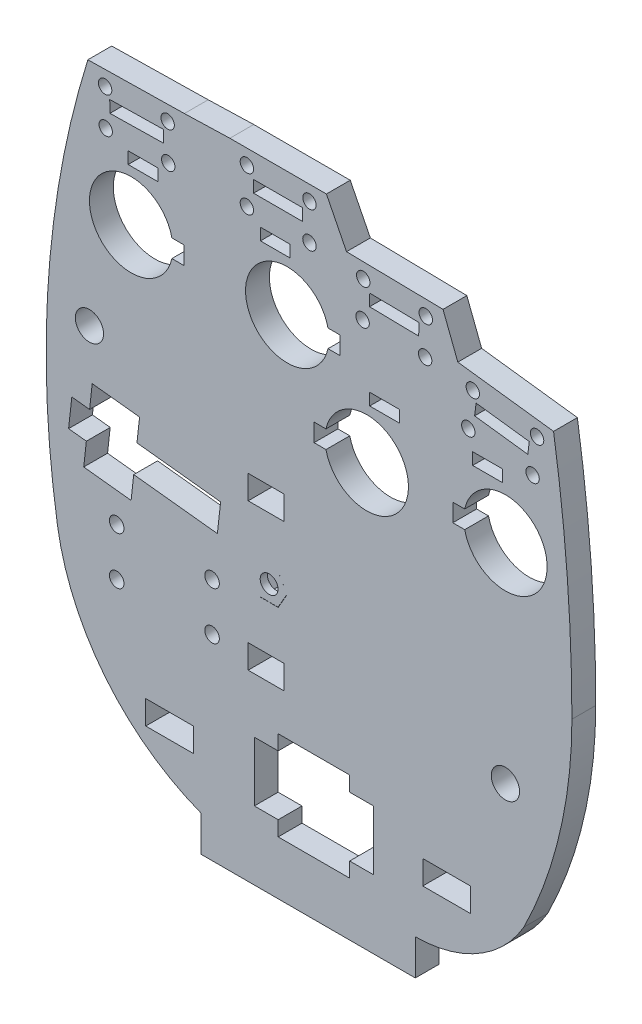
SolidWorks part; units mm, degrees
ref_plane "Front Plane" through (0, 0, 0) normal (0, 0, 1) x (1, 0, 0)
ref_plane "Top Plane" through (0, 0, 0) normal (0, 1, 0) x (1, 0, 0)
ref_plane "Right Plane" through (0, 0, 0) normal (1, 0, 0) x (0, 0, -1)
sketch "Sketch1" plane through (0, 0, 0) normal (0, 0, 1) x (1, 0, 0)
  line L0 (-4.125, 78.51) -> (-4.125, 76.51)
  line L1 (4.125, 78.51) -> (-4.125, 78.51)
  line L2 (-12.9786, -18) -> (-12.9786, -24)
  line L3 (-10.203, 23.9877) -> (-9.6615, 28.8655)
  line L4 (-4.125, 76.51) -> (4.125, 76.51)
  line L5 (4.125, 76.51) -> (4.125, 78.51)
  line L6 (-35.1781, 26.7603) -> (-34.6366, 31.6381)
  line L7 (10.3588, 63.1512) -> (10.3588, 60.1512)
  line L8 (-8.1, 82.51) -> (8.1, 82.51)
  line L9 (8.3588, 63.1512) -> (10.3588, 63.1512)
  line L10 (11.4712, 75.8064) -> (27.6688, 75.5236)
  line L11 (32.6473, 57.3216) -> (37.6473, 57.3216)
  line L12 (0, 0) -> (-23.845, 0) construction
  line L13 (10.3588, 60.1512) -> (8.3588, 60.1512)
  line L14 (-17.8416, 63.1512) -> (-15.8416, 63.1512)
  line L15 (-15.8416, 63.1512) -> (-15.8416, 60.1512)
  line L16 (-15.8416, 60.1512) -> (-17.8416, 60.1512)
  line L17 (32.6473, 55.3216) -> (37.6473, 55.3216)
  line L18 (37.6473, 55.3216) -> (37.6473, 57.3216)
  line L19 (32.6473, 57.3216) -> (32.6473, 55.3216)
  line L20 (-28.2745, 78.062) -> (-19.2758, 78.2192)
  line L21 (-28.2745, 78.062) -> (-28.2395, 76.0623)
  line L22 (-10.0543, 52.8756) -> (-18.0543, 52.8756) construction
  line L23 (-9.6615, 28.8655) -> (-23.7037, 30.4244)
  line L24 (-28.2395, 76.0623) -> (-19.2408, 76.2195)
  line L25 (-24.6866, 21.571) -> (-32.6377, 22.4537)
  line L26 (-32.6377, 22.4537) -> (-32.1964, 26.4293)
  line L27 (-24.2452, 25.5466) -> (-10.203, 23.9877)
  line L28 (-19.2408, 76.2195) -> (-19.2758, 78.2192)
  line L29 (15.3631, 57.3216) -> (20.3631, 57.3216)
  line L30 (15.3631, 55.3216) -> (20.3631, 55.3216)
  line L31 (-12.9786, -24) -> (23.0214, -24)
  line L32 (20.3631, 55.3216) -> (20.3631, 57.3216)
  line L33 (23.0214, -24) -> (23.0214, -18)
  line L34 (15.3631, 57.3216) -> (15.3631, 55.3216)
  line L35 (-2.9786, 72.1512) -> (2.0214, 72.1512)
  line L36 (15.3758, 71.7376) -> (15.3409, 69.7379)
  line L37 (15.3409, 69.7379) -> (23.5897, 69.5939)
  line L38 (8.0257, 48.3216) -> (6.0257, 48.3216)
  line L39 (-2.9786, 70.1512) -> (2.0214, 70.1512)
  line L40 (23.6246, 71.5936) -> (15.3758, 71.7376)
  line L41 (6.0257, 48.3216) -> (6.0257, 45.3216)
  line L42 (23.5897, 69.5939) -> (23.6246, 71.5936)
  line L43 (-23.845, 0) -> (-23.845, 82.14) construction
  line L44 (2.0214, 70.1512) -> (2.0214, 72.1512)
  line L45 (19.57, 75.665) -> (19.6234, 78.7251) construction
  line L46 (-2.9786, 72.1512) -> (-2.9786, 70.1512)
  line L47 (42.1536, 63.5476) -> (33.2239, 64.6755)
  line L48 (6.0257, 45.3216) -> (8.0257, 45.3216)
  line L49 (29.3099, 45.3216) -> (31.3099, 45.3216)
  line L50 (29.3099, 48.3216) -> (29.3099, 45.3216)
  line L51 (31.3099, 48.3216) -> (29.3099, 48.3216)
  line L52 (-23.2624, 34.3999) -> (-31.2135, 35.2826)
  line L53 (33.2239, 64.6755) -> (32.9732, 62.6912)
  line L54 (-25.179, 72.1512) -> (-20.179, 72.1512)
  line L55 (-31.9438, 81.9985) -> (-15.7462, 82.2815)
  line L56 (46.2262, 67.065) -> (30.1538, 69.095)
  line L57 (-25.179, 70.1512) -> (-20.179, 70.1512)
  line L58 (32.9732, 62.6912) -> (41.903, 61.5633)
  line L59 (-20.179, 70.1512) -> (-20.179, 72.1512)
  line L60 (-25.179, 72.1512) -> (-25.179, 70.1512)
  line L61 (41.903, 61.5633) -> (42.1536, 63.5476)
  line L62 (-35.1781, 26.7603) -> (-32.1964, 26.4293)
  line L63 (-4, -2.5) -> (0, -2.5)
  line L64 (12, 0) -> (0, 0)
  line L65 (12, 0) -> (12, -2.5)
  line L66 (12, -15) -> (0, -15)
  line L67 (-31.2135, 35.2826) -> (-31.6549, 31.3071)
  line L68 (-23.7037, 30.4244) -> (-23.2624, 34.3999)
  line L69 (-34.6366, 31.6381) -> (-31.6549, 31.3071)
  line L70 (-24.6866, 21.571) -> (-24.2452, 25.5466)
  line L71 (16, -7.5) -> (41.235, -7.5) construction
  line L72 (0, -15) -> (0, -12.5)
  line L73 (-4, -12.5) -> (-4, -2.5)
  line L74 (-4, -12.5) -> (0, -12.5)
  line L75 (0, -2.5) -> (0, 0)
  line L76 (0, 0) -> (0, 82.51) construction
  line L77 (-22.0543, 52.8756) -> (-27.0543, 52.8756) construction
  line L78 (-10.0543, -2.1244) -> (-18.0543, -2.1244) construction
  line L79 (-22.0543, -2.1244) -> (-27.0543, -2.1244) construction
  line L80 (0, 0) -> (19.57, 0) construction
  line L81 (16, -12.5) -> (12, -12.5)
  line L82 (16, -12.5) -> (16, -2.5)
  line L83 (16, -2.5) -> (12, -2.5)
  line L84 (12, -12.5) -> (12, -15)
  line L85 (-9.9323, 26.4266) -> (5.8267, 24.6771) construction
  line L86 (0, 23.5609) -> (-3, 23.5609)
  line L87 (-3, 23.5609) -> (-4.5, 20.9629)
  line L88 (-4.5, 20.9629) -> (-3, 18.3648)
  line L89 (19.57, 0) -> (19.57, 75.665) construction
  line L90 (0, 0) -> (38.19, 0) construction
  line L91 (38.19, 0) -> (38.19, 68.08) construction
  line L92 (30.1538, 69.095) -> (27.6688, 75.5236)
  line L93 (11.4712, 75.8064) -> (8.1, 82.51)
  line L94 (-8.1, 82.51) -> (-15.7462, 82.2815)
  line L95 (-35.1781, 26.7603) -> (49.3063, 26.7603) construction
  line L96 (37.6888, 64.1115) -> (38.19, 68.08) construction
  line L97 (-3, 18.3648) -> (0, 18.3648)
  line L98 (0, 18.3648) -> (1.5, 20.9629)
  line L99 (1.5, 20.9629) -> (0, 23.5609)
  line L100 (0, 18.3648) -> (-3, 23.5609) construction
  line L101 (0, 23.5609) -> (-3, 18.3648) construction
  line L102 (38.1473, 11.8216) -> (-37.0527, 11.8216) construction
  line L103 (-29.0506, 79.5486) -> (-31.9001, 79.4989) construction
  line L104 (0.9634, 10.717) -> (0.9634, 6.717)
  line L105 (0.9634, 6.717) -> (-5.0366, 6.717)
  line L106 (-5.0366, 6.717) -> (-5.0366, 10.717)
  line L107 (-5.0366, 10.717) -> (0.9634, 10.717)
  line L108 (-5.0366, 31.3356) -> (0.9634, 31.3356)
  line L109 (-5.0366, 35.3356) -> (-5.0366, 31.3356)
  line L110 (0.9634, 35.3356) -> (-5.0366, 35.3356)
  line L111 (0.9634, 31.3356) -> (0.9634, 35.3356)
  line L112 (-31.9001, 79.4989) -> (-31.9438, 81.9985) construction
  line L113 (-18.5521, 79.732) -> (-15.7025, 79.7819) construction
  line L114 (-15.7025, 79.7819) -> (-15.7462, 82.2815) construction
  line L115 (-23.7751, 78.1406) -> (-23.845, 82.14) construction
  line L116 (5.25, 80.01) -> (8.1, 80.01) construction
  line L117 (8.1, 80.01) -> (8.1, 82.51) construction
  line L118 (-5.25, 80.01) -> (-8.1, 80.01) construction
  line L119 (-22.0543, 0.2506) -> (-27.0543, 0.2506) construction
  line L120 (-8.1, 80.01) -> (-8.1, 82.51) construction
  line L121 (-10.0543, 1.8756) -> (-10.0543, -2.1244) construction
  line L122 (32.6681, 66.2576) -> (29.8406, 66.6147) construction
  line L123 (-10.0543, 52.8756) -> (-10.0543, 46.8756) construction
  line L124 (-10.0543, 1.8756) -> (-18.0543, 1.8756) construction
  line L125 (-18.0543, 1.8756) -> (-18.0543, -2.1244) construction
  line L126 (29.8406, 66.6147) -> (30.1538, 69.095) construction
  line L127 (14.2772, 73.257) -> (11.4276, 73.3067) construction
  line L128 (-22.0543, 0.2506) -> (-22.0543, -2.1244) construction
  line L129 (-27.0543, 0.2506) -> (-27.0543, -2.1244) construction
  line L130 (32.6681, 66.2576) -> (31.9162, 60.3049) construction
  line L131 (-10.0543, 46.8756) -> (-18.0543, 46.8756) construction
  line L132 (-27.0543, 52.8756) -> (-27.0543, 50.5006) construction
  line L133 (-18.0543, 46.8756) -> (-18.0543, 52.8756) construction
  line L134 (11.4712, 75.8064) -> (11.4276, 73.3067) construction
  line L135 (-22.0543, 6.717) -> (-22.0543, 10.717) construction
  line L136 (-22.0543, 10.717) -> (-27.0543, 10.717) construction
  line L137 (-27.0543, 50.5006) -> (-22.0543, 50.5006) construction
  line L138 (-22.0543, 52.8756) -> (-22.0543, 50.5006) construction
  line L139 (-27.0543, 10.717) -> (-27.0543, 6.717) construction
  line L140 (-27.0543, 6.717) -> (-22.0543, 6.717) construction
  line L141 (-27.0543, 38.7272) -> (-22.0543, 38.7272) construction
  line L142 (-22.0543, 38.7272) -> (-22.0543, 42.7272) construction
  line L143 (-22.0543, 42.7272) -> (-27.0543, 42.7272) construction
  line L144 (-27.0543, 42.7272) -> (-27.0543, 38.7272) construction
  line L145 (24.7756, 73.0738) -> (27.6251, 73.024) construction
  line L146 (27.6251, 73.024) -> (27.6688, 75.5236) construction
  line L147 (43.4577, 64.8948) -> (46.2853, 64.5376) construction
  line L148 (43.4577, 64.8948) -> (42.7059, 58.9421) construction
  line L149 (42.7059, 58.9421) -> (45.5334, 58.5849) construction
  line L150 (45.5334, 58.5849) -> (46.2853, 64.5376) construction
  line L151 (24.7756, 73.0738) -> (24.6709, 67.0747) construction
  line L152 (14.2772, 73.257) -> (14.1725, 67.2579) construction
  line L153 (-18.5521, 79.732) -> (-18.4473, 73.733) construction
  line L154 (-29.0506, 79.5486) -> (-28.9458, 73.5496) construction
  line L155 (38.1473, 46.8216) -> (38.1473, 11.8216) construction
  line L156 (-31.6, 35.8756) -> (-31.6, -2.1244) construction
  line L157 (-31.6, -2.1244) -> (-6.6, -2.1244) construction
  line L158 (-6.6, -2.1244) -> (-6.6, 35.8756) construction
  line L159 (-6.6, 35.8756) -> (-31.6, 35.8756) construction
  arc A0 (-37.0527, 11.8216) -> (-31.9438, 81.9985) centre (115.9422, 35.958) cw
  circle A1 centre (-1.5, 20.9629) radius 4.5 construction
  arc A2 (8.3588, 63.1512) -> (8.3588, 60.1512) centre (1.5214, 61.6512) ccw
  arc A3 (8.0257, 45.3216) -> (8.0257, 48.3216) centre (14.8631, 46.8216) ccw
  arc A4 (-17.8416, 63.1512) -> (-17.8416, 60.1512) centre (-24.679, 61.6512) ccw
  arc A5 (31.3099, 45.3216) -> (31.3099, 48.3216) centre (38.1473, 46.8216) ccw
  arc A6 (23.0214, -18) -> (41.235, -7.5) centre (23.0214, 3.0469) ccw
  arc A7 (49.3063, 26.7603) -> (41.235, -7.5) centre (-27.4409, 26.7603) cw
  arc A8 (-37.0527, 11.8216) -> (-12.9786, -18) centre (0.8651, 17.8035) ccw
  arc A9 (49.3063, 26.7603) -> (46.2262, 67.065) centre (-215.9296, 26.7603) ccw
  circle A10 centre (-27.1, 24.8756) radius 1.225 construction
  circle A11 centre (38.1473, 11.8216) radius 2.375
  circle A12 centre (-14, -9.1244) radius 2.375 construction
  circle A13 centre (-27.1, 8.8756) radius 1.225
  circle A14 centre (-27.1, 16.8756) radius 1.225
  circle A15 centre (-11.1, 8.8756) radius 1.225
  circle A16 centre (-11.1, 16.8756) radius 1.225
  circle A17 centre (-11.1, 24.8756) radius 1.225 construction
  circle A18 centre (-5.25, 80.01) radius 1.125
  circle A19 centre (32.6681, 66.2576) radius 1.125
  circle A22 centre (-31.6815, 43.4564) radius 2.375
  circle A49 centre (5.25, 80.01) radius 1.125
  circle A50 centre (5.25, 74.01) radius 1.125
  circle A51 centre (-5.25, 74.01) radius 1.125
  circle A52 centre (-29.0506, 79.5486) radius 1.125
  circle A53 centre (-18.5521, 79.732) radius 1.125
  circle A54 centre (-28.9458, 73.5496) radius 1.125
  circle A55 centre (-18.4473, 73.733) radius 1.125
  circle A56 centre (24.6709, 67.0747) radius 1.125
  circle A57 centre (14.1725, 67.2579) radius 1.125
  circle A58 centre (24.7756, 73.0738) radius 1.125
  circle A59 centre (14.2772, 73.257) radius 1.125
  circle A60 centre (31.9162, 60.3049) radius 1.125
  circle A61 centre (43.4577, 64.8948) radius 1.125
  circle A63 centre (42.7059, 58.9421) radius 1.125
  dimension "D1" = 4.75
  dimension "D2" = 2.25
  dimension "D11" = 1.5214
  dimension "D12" = 2.0214
  dimension "D16" = 6.0257
  dimension "D17" = 4
  dimension "D18" = 8.3588
  dimension "D19" = 23.845
  dimension "D22" = 4
  dimension "D23" = 19.57
  dimension "D24" = 75.665
  dimension "D25" = 12
  dimension "D35" = 4
  dimension "D36" = 16.2
  dimension "D37" = 2
  dimension "D38" = 29.3099
  dimension "D39" = 2.85
  dimension "D40" = 46.8216
  dimension "D43" = 2.85
  dimension "D44" = 24.679
  dimension "D45" = 9
  dimension "D46" = 0.7292
  dimension "D47" = 4.9078
  dimension "D49" = 5.0366
  dimension "D51" = 10.203
  dimension "D55" = 24
  dimension "D56" = 15.8416
  dimension "D13" = 4
  dimension "D58" = 2.5
  dimension "D59" = 18.0543
  dimension "D60" = 8.1
  dimension "D61" = 6
  dimension "D63" = 22.0543
  dimension "D65" = 2.85
  dimension "D52" = 10.0543
  dimension "D48" = 25.1285
  dimension "D53" = 12.9786
  dimension "D57" = 4
  dimension "D69" = 6
  dimension "D70" = 2.5
  dimension "D71" = 1.8756
  dimension "D79" = 43.4564
  dimension "D82" = 55.3216
  dimension "D67" = 2.5
  dimension "D68" = 31.6815
  dimension "D92" = 8
  dimension "D5" = 7
  dimension "D29" = 2.5
  dimension "D83" = 8.1
  dimension "D85" = 2
  dimension "D87" = 38
  dimension "D89" = 2.45
  dimension "D10" = 0.9634
  dimension "D14" = 82.51
  dimension "D15" = 3
  dimension "D20" = 10
  dimension "D21" = 82.14
  dimension "D26" = 15.3631
  dimension "D27" = 2.5
  dimension "D28" = 0
  dimension "D30" = 20.3631
  dimension "D31" = 38.19
  dimension "D32" = 68.08
  dimension "D33" = 23.0214
  dimension "D34" = 6
  dimension "D41" = 14.8631
  dimension "D42" = 32.6473
  dimension "D50" = 9.6615
  dimension "D54" = 14
  dimension "D62" = 20.179
  dimension "D66" = 2.85
  dimension "D72" = 6.717
  dimension "D73" = 9.0001
  dimension "D74" = 9.0007
  dimension "D75" = 35
  dimension "D76" = 21.571
  dimension "D77" = 31.3356
  dimension "D78" = 6
  dimension "D80" = 45.3216
  dimension "D81" = 46.8756
  dimension "D84" = 60.1512
  dimension "D86" = 70.1512
  dimension "D88" = 25
  dimension "D90" = 6.6
  dimension "D91" = 2.1244
  dimension "D93" = 9.1244
  dimension "D94" = 16
  dimension "D95" = 8
  dimension "D96" = 4.5
  dimension "D97" = 2
extrude "Boss-Extrude1" add sketch "Sketch1" along normal blind 4
sketch "Sketch3" plane through (0, 0, 0) normal (0, 0, -1) x (-1, 0, 0)
  line L1 (-24.2714, -10) -> (-32.2714, -10)
  line L2 (-32.2714, -10) -> (-32.2714, -6)
  line L3 (-32.2714, -6) -> (-24.2714, -6)
  line L4 (-24.2714, -6) -> (-24.2714, -10)
  line L5 (-5.0214, -24) -> (-5.0214, -4.0378) construction
  line L6 (12.9786, -24) -> (-23.0214, -24) construction
  line L7 (14.2286, -6) -> (14.2286, -10)
  line L8 (22.2286, -6) -> (14.2286, -6)
  line L9 (22.2286, -10) -> (22.2286, -6)
  line L10 (14.2286, -10) -> (22.2286, -10)
  dimension "D1" = 4
  dimension "D2" = 8
  dimension "D3" = 14
  dimension "D4" = 19.25
extrude "Cut-Extrude2" cut sketch "Sketch3" against normal through all
sketch "Sketch4" plane through (0, 0, 0) normal (0, 0, -1) x (-1, 0, 0)
  line L0 (19.1, 16.8756) -> (19.1, 8.8756) construction
  circle A0 centre (27.1, 16.8756) radius 2.1
  circle A1 centre (27.1, 8.8756) radius 2.1
  circle A2 centre (11.1, 8.8756) radius 2.1
  circle A3 centre (11.1, 16.8756) radius 2.1
  dimension "D1" = 4.2
extrude "Cut-Extrude3" cut sketch "Sketch4" against normal blind 2
sketch "Sketch2" plane through (0, 0, 4) normal (0, 0, 1) x (1, 0, 0)
  line L1 (-19.1, 16.8756) -> (-19.1, 8.8756) construction
  circle A0 centre (-11.1, 16.8756) radius 2.1
  circle A1 centre (-11.1, 8.8756) radius 2.1
  circle A2 centre (-27.1, 8.8756) radius 2.1
  circle A3 centre (-27.1, 16.8756) radius 2.1
  dimension "D1" = 4.2
  dimension "D2" = 27.1
extrude "Cut-Extrude1" [suppressed] cut sketch "Sketch2" against normal blind 2
sketch "Sketch5" plane through (0, 0, 4) normal (0, 0, 1) x (1, 0, 0)
  line L0 (-10.203, 24.0723) -> (-9.6615, 28.8655) construction
  line L1 (-3.0188, 18.3917) -> (-0.0188, 18.3917)
  line L2 (-0.0188, 18.3917) -> (1.4812, 20.9898)
  line L3 (1.4812, 20.9898) -> (-0.0188, 23.5878)
  line L4 (-0.0188, 23.5878) -> (-3.0188, 23.5878)
  line L5 (-3.0188, 23.5878) -> (-4.5188, 20.9898)
  line L6 (-4.5188, 20.9898) -> (-3.0188, 18.3917)
  line L7 (-9.9323, 26.4689) -> (6.8213, 24.5762) construction
  line L9 (-35.1872, 26.7613) -> (-34.6457, 31.6391) construction
  line L10 (-23.2609, 34.4137) -> (-23.7037, 30.4244) construction
  line L11 (-24.685, 21.585) -> (-32.6362, 22.4677) construction
  line L12 (-32.6362, 22.4677) -> (-32.1964, 26.4293) construction
  line L13 (-24.2452, 25.5466) -> (-9.6818, 23.9298) construction
  line L14 (-23.2609, 34.4137) -> (-31.212, 35.2964) construction
  line L15 (-35.1872, 26.7613) -> (-32.1964, 26.4293) construction
  line L16 (-23.7037, 30.4244) -> (-9.6615, 28.8655) construction
  line L17 (-24.685, 21.585) -> (-24.2452, 25.5466) construction
  line L18 (-34.6457, 31.6391) -> (-31.6549, 31.3071) construction
  line L19 (-31.6549, 31.3071) -> (-31.212, 35.2964) construction
  line L20 (-9.6615, 28.8655) -> (-23.7037, 30.4244) construction
  circle A0 centre (-1.5188, 20.9898) radius 4.5 construction
  circle A1 centre (-1.5188, 20.9898) radius 1.5
  dimension "D1" = 2.5981
  dimension "D3" = 3
  dimension "D6" = 9
  dimension "D7" = 4.9078
  dimension "D2" = 1.5
  dimension "D4" = 9.6615
  dimension "D5" = 10.203
  dimension "D8" = 25.1285
  dimension "D9" = 24.0723
extrude "Boss-Extrude2" add sketch "Sketch5" against normal blind 1.2
equation "\"D14@Sketch1\"= \"HL@parametersSketch@prostheticParameters.SLDPRT\" * 0.446'Mioddle Base Frame "
equation "\"D19@Sketch1\"= \"HB@parametersSketch@prostheticParameters.SLDPRT\" * 0.251'Index Base Frame X"
equation "\"D21@Sketch1\"= \"HL@parametersSketch@prostheticParameters.SLDPRT\" * 0.444'Index Base Frame Y"
equation "\"D23@Sketch1\"= \"HB@parametersSketch@prostheticParameters.SLDPRT\" * 0.206'Ring Base Frame X"
equation "\"D24@Sketch1\"= \"HL@parametersSketch@prostheticParameters.SLDPRT\" * 0.409'Ring Base Frame Y"
equation "\"D31@Sketch1\"= \"HB@parametersSketch@prostheticParameters.SLDPRT\" * 0.402'Pinky Base Frame X"
equation "\"D32@Sketch1\"= \"HL@parametersSketch@prostheticParameters.SLDPRT\" * 0.368'Pinky Base Frame Y"
equation "\"D36@Sketch1\"= \"fingerWidth@parametersSketch@prostheticParameters.SLDPRT\"'Fingers Width"
equation "\"D76@Sketch1\"= \"HL@parametersSketch@prostheticParameters.SLDPRT\" * 0.1166'Hole Thumb Y"
equation "\"D51@Sketch1\"= \"HB@parametersSketch@prostheticParameters.SLDPRT\" * 0.1074'Hole Thumb X1"
equation "\"D50@Sketch1\" = \"HB@parametersSketch@prostheticParameters.SLDPRT\" * 0.1017'Hole Thumb X2"
equation "\"D73@Sketch1\"=(\"fingerWidth@parametersSketch@prostheticParameters.SLDPRT\" * 0.55556)"
equation "\"D74@Sketch1\"=(\"fingerWidth@parametersSketch@prostheticParameters.SLDPRT\" * 0.5556)"
equation "\"D60@Sketch1\"= \"fingerWidth@parametersSketch@prostheticParameters.SLDPRT\" / 2"
equation "\"D83@Sketch1\"= \"fingerWidth@parametersSketch@prostheticParameters.SLDPRT\" / 2"
equation "\"D1@Sketch1\"= 4.45 + \"tol1@parametersSketch@prostheticParameters.SLDPRT\""
equation "\"D2@Sketch1\"= 1.95 + \"tol1@parametersSketch@prostheticParameters.SLDPRT\""
equation "\"D4@Sketch5\"= \"D50@Sketch1\"'Support nut"
equation "\"D5@Sketch5\"= \"D51@Sketch1\"'Support Nut"
